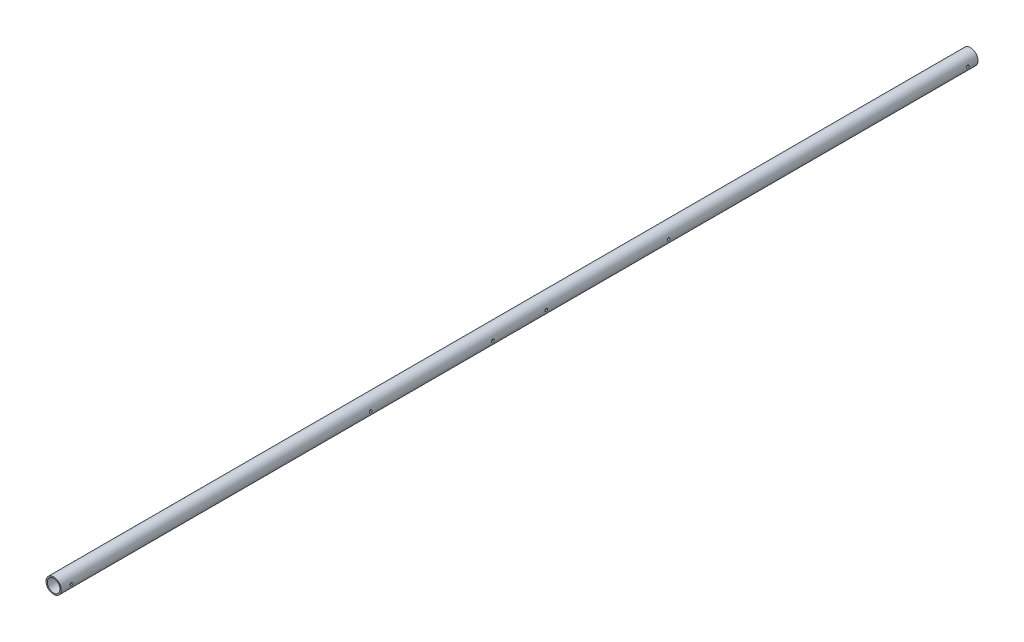
SolidWorks part; units mm, degrees
material "Plain Carbon Steel"
ref_plane "Front Plane" through (0, 0, 0) normal (0, 0, 1) x (1, 0, 0)
ref_plane "Top Plane" through (0, 0, 0) normal (0, 1, 0) x (1, 0, 0)
ref_plane "Right Plane" through (0, 0, 0) normal (1, 0, 0) x (0, 0, -1)
sketch "Sketch1" plane through (0, 0, 0) normal (0, 0, 1) x (1, 0, 0)
  circle A0 centre (0, 0) radius 19.05
  circle A1 centre (0, 0) radius 15.875
  dimension "D1" = 38.1
  dimension "D2" = 3.175
extrude "Boss-Extrude1" add sketch "Sketch1" along normal mid plane 2286
ref_plane "Plane1" through (19.05, 0, 0) normal (1, 0, 0) x (0, 0, -1)
sketch "Sketch2" plane through (19.05, 0, 0) normal (1, 0, 0) x (0, 0, -1)
  line L0 (-1143, 19.05) -> (-1143, -19.05) construction
  line L1 (-1143, 19.05) -> (-1143, -19.05)
  line L2 (0, 0) -> (0, -50000) construction
  point P0 (-1117.6, 0)
  point P3 (-1143, 0)
  point P4 (-66.675, 0)
  point P8 (66.675, 0)
  point P9 (1117.6, 0)
  point P10 (-371.475, 0)
  point P12 (371.475, 0)
  dimension "D1" = 66.675
  dimension "D2" = 25.4
  dimension "D3" = 304.8
hole_wizard "1/4 Clearance Hole1" positions "Sketch4" profile "Sketch5" hole size "1/4" standard "ANSI Inch" end condition through all
sketch "Sketch4" plane through (19.05, 0, 0) normal (1, 0, 0) x (0, 0, -1)
  point P0 (-1117.6, 0)
  point P4 (-66.675, 0)
  point P6 (66.675, 0)
  point P9 (1117.6, 0)
  point P13 (371.475, 0)
  point P15 (-371.475, 0)
sketch "Sketch5" plane through (19.05, 0, 1117.6) normal (0, 1, 0) x (0, 0, -1)
  line L0 (0, 0) -> (0, 38.1)
  line L1 (0, 38.1) -> (3.3782, 38.1)
  line L2 (3.3782, 38.1) -> (3.3782, 0)
  line L5 (3.3782, 0) -> (0, 0)
  line L11 (0, -6.35) -> (0, 107.95) construction
  dimension "Thru Hole Dia." = 6.7564
  dimension "Thru Hole Depth" = 38.1
ref_plane "Plane2" through (0, 0, 66.675) normal (0, 0, 1) x (1, 0, 0)
ref_plane "Plane3" through (0, 0, -66.675) normal (0, 0, 1) x (1, 0, 0)
ref_plane "Plane4" through (0, 0, 762) normal (0, 0, 1) x (1, 0, 0)
ref_plane "Plane5" through (0, 0, 1066.8) normal (0, 0, 1) x (1, 0, 0)
